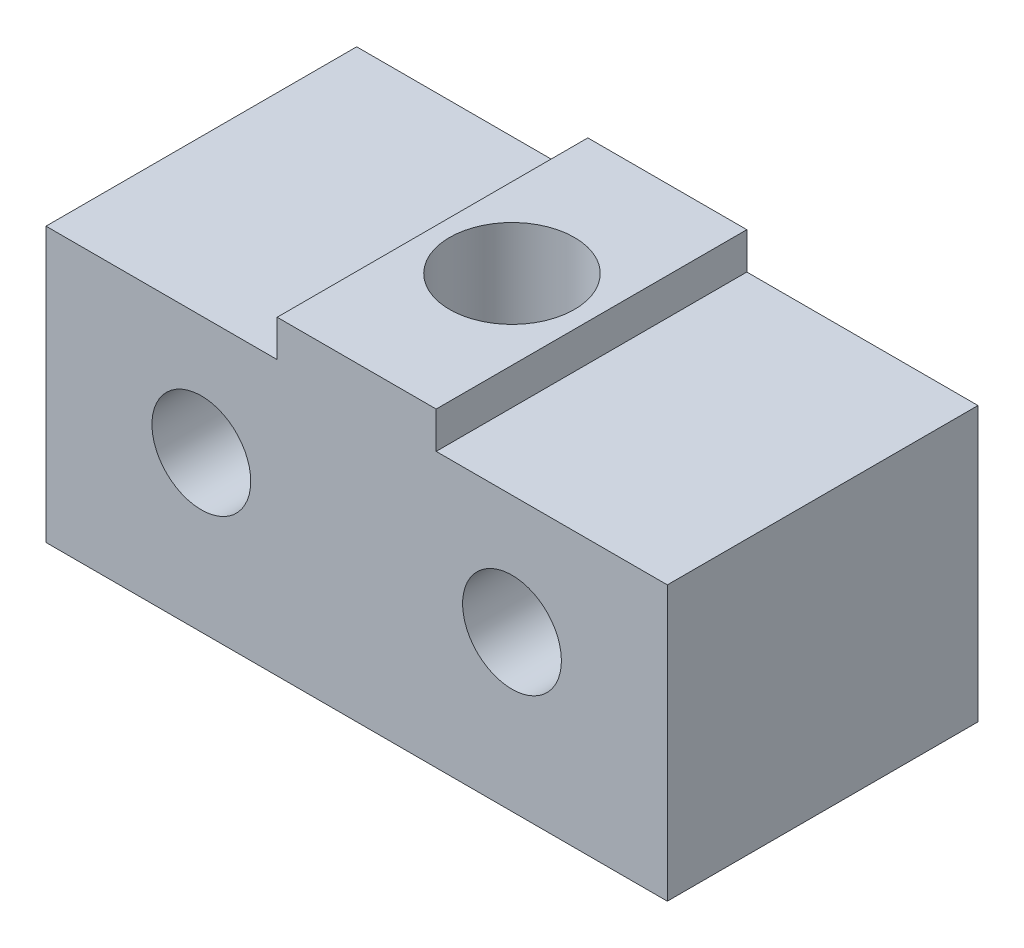
SolidWorks part; units mm, degrees
ref_plane "Front Plane" through (0, 0, 0) normal (0, 0, 1) x (1, 0, 0)
ref_plane "Top Plane" through (0, 0, 0) normal (0, 1, 0) x (1, 0, 0)
ref_plane "Right Plane" through (0, 0, 0) normal (1, 0, 0) x (0, 0, -1)
sketch "Sketch5" plane through (0, 0, 0) normal (0, 0, 1) x (1, 0, 0)
  line L1 (0, 0) -> (-25.4, 0)
  line L2 (0, 0) -> (0, -12.7)
  line L3 (0, -12.7) -> (-25.4, -12.7)
  line L4 (-25.4, 0) -> (-25.4, -12.7)
  dimension "D1" = 25.4
  dimension "D2" = 12.7
extrude "Boss-Extrude2" add sketch "Sketch5" along normal blind 12.7
sketch "Sketch6" plane through (0, 0, 12.7) normal (0, 0, 1) x (1, 0, 0)
  line L0 (-12.7, 0) -> (-12.7, -12.7) construction
  line L1 (0, 0) -> (-25.4, 0) construction
  line L2 (-25.4, -12.7) -> (0, -12.7) construction
  line L3 (-25.4, -6.35) -> (0, -6.35) construction
  line L4 (-25.4, 0) -> (-25.4, -12.7) construction
  line L5 (0, -12.7) -> (0, 0) construction
  line L7 (-25.4, 0) -> (-15.95, 0)
  line L8 (-25.4, 0) -> (-25.4, -1.5)
  line L9 (-25.4, -1.5) -> (-15.95, -1.5)
  line L10 (-15.95, 0) -> (-15.95, -1.5)
  line L11 (0, 0) -> (-9.45, 0)
  line L12 (0, 0) -> (0, -1.5)
  line L13 (0, -1.5) -> (-9.45, -1.5)
  line L14 (-9.45, 0) -> (-9.45, -1.5)
  line L15 (-19.05, 0) -> (-19.05, -12.7) construction
  line L16 (-6.35, 0) -> (-6.35, -12.7) construction
  dimension "D1" = 1.5
  dimension "D2" = 1.5
  dimension "D3" = 3.25
  dimension "D4" = 3.25
  dimension "D5" = 12.7
  dimension "D6" = 6.35
  dimension "D7" = 6.35
hole_wizard "#10-32 Tapped Hole1" positions "Sketch9" profile "Sketch10" tap size "#10-32" standard "ANSI Inch" end condition through all
sketch "Sketch9" plane through (0, 0, 12.7) normal (0, 0, 1) x (1, 0, 0)
  line L0 (-19.05, 0) -> (-19.05, -12.7) construction
  line L1 (-25.4, -6.35) -> (0, -6.35) construction
  point P0 (-19.05, -6.35)
sketch "Sketch10" plane through (-19.05, -6.35, 12.7) normal (1, 0, 0) x (0, -1, 0)
  line L0 (0, 0) -> (0, 12.7)
  line L1 (0, 12.7) -> (2.0193, 12.7)
  line L2 (2.0193, 12.7) -> (2.0193, 0)
  line L5 (2.0193, 0) -> (0, 0)
  line L11 (0, -6.35) -> (0, 107.95) construction
  dimension "Thread Major Dia." = 4.0386
  dimension "Thru Tap Drill Depth" = 12.7
ref_plane "Plane1" through (-12.7, 0, 0) normal (-1, 0, 0) x (0, 0, 1)
mirror "Mirror1" about plane through (-12.7, 0, 0) normal (-1, 0, 0) of "#10-32 Tapped Hole1"
extrude "Cut-Extrude1" cut sketch "Sketch6" against normal up to surface (12.7 mm away) up to face at (-4.3307, -6.35, 0)
sketch "Sketch11" plane through (0, 0, 0) normal (0, 1, 0) x (1, 0, 0)
  line L0 (-15.95, -6.35) -> (-9.45, -6.35) construction
  line L1 (-15.95, 0) -> (-15.95, -12.7) construction
  line L2 (-9.45, 0) -> (-9.45, -12.7) construction
  line L3 (-12.7, 0) -> (-12.7, -12.7) construction
  line L4 (-9.45, 0) -> (-15.95, 0) construction
  line L5 (-9.45, -12.7) -> (-15.95, -12.7) construction
  circle A0 centre (-12.7, -6.35) radius 2.5
hole_wizard "CBORE for #10 Socket Head Cap Screw2" positions "Sketch15" profile "Sketch16" counterbore size "#10" standard "ANSI Inch" end condition through all
sketch "Sketch15" plane through (0, -12.7, 0) normal (0, -1, 0) x (-1, 0, 0)
  line L0 (15.95, -6.35) -> (9.45, -6.35) construction
  line L1 (12.7, 0) -> (12.7, -12.7) construction
  point P0 (12.7, -6.35)
sketch "Sketch16" plane through (-12.7, -12.7, 6.35) normal (1, 0, 0) x (0, 0, -1)
  line L0 (0, 0) -> (0, 12.7)
  line L1 (0, 12.7) -> (2.5527, 12.7)
  line L3 (2.5527, 12.7) -> (2.5527, 4.826)
  line L4 (2.5527, 4.826) -> (4.7625, 4.826)
  line L5 (4.7625, 4.826) -> (4.7625, 0)
  line L7 (4.7625, 0) -> (0, 0)
  line L11 (0, -6.35) -> (0, 107.95) construction
  dimension "Thru Hole Dia." = 5.1054
  dimension "Thru Hole Depth" = 12.7
  dimension "C'Bore Dia." = 9.525
  dimension "C'Bore Depth" = 4.826
